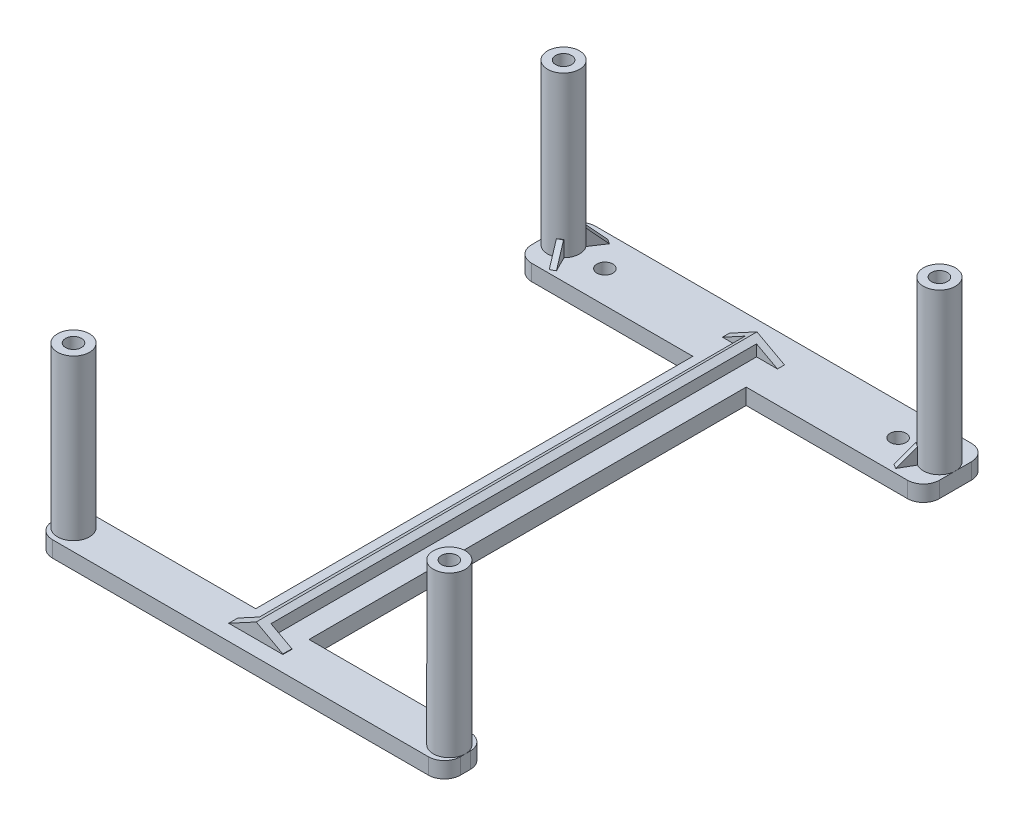
SolidWorks part; units mm, degrees
ref_plane "前视基准面" through (0, 0, 0) normal (0, 0, 1) x (1, 0, 0)
ref_plane "上视基准面" through (0, 0, 0) normal (0, 1, 0) x (1, 0, 0)
ref_plane "右视基准面" through (0, 0, 0) normal (1, 0, 0) x (0, 0, -1)
sketch "草图1" plane through (0, 0, 0) normal (0, 1, 0) x (1, 0, 0)
  line L0 (-39.882, 2.8841) -> (30.618, 2.8841)
  line L1 (-39.882, 2.8841) -> (-39.882, -9.1159)
  line L2 (30.618, 2.8841) -> (30.618, -9.1159)
  line L3 (-39.882, -9.1159) -> (30.618, -9.1159)
  circle A0 centre (-32.132, -3.1159) radius 1.5
  circle A1 centre (22.868, -3.1159) radius 1.5
  dimension "D3" = 3
  dimension "D4" = 6
  dimension "D6" = 3
  dimension "D1" = 12
  dimension "D2" = 70.5
  dimension "D5" = 7.75
  dimension "D7" = 7.75
  dimension "D8" = 6
extrude "凸台-拉伸2" add sketch "草图1" along normal blind 4
sketch "草图3" plane through (0, 0, 0) normal (0, -1, 0) x (1, 0, 0)
  line L2 (-9.632, 91.1159) -> (-9.632, 9.1159)
  line L3 (-9.632, 91.1159) -> (0.368, 91.1159)
  line L4 (-9.632, 9.1159) -> (0.368, 9.1159)
  line L5 (0.368, 91.1159) -> (0.368, 9.1159)
  dimension "D1" = 82
extrude "凸台-拉伸3" add sketch "草图3" against normal blind 3
sketch "草图4" plane through (0, 3, 0) normal (0, 1, 0) x (1, 0, 0)
  line L0 (-4.632, -91.1159) -> (-39.882, -91.1159)
  line L1 (0.368, -91.1159) -> (-9.632, -91.1159) construction
  line L2 (-4.632, -91.1159) -> (30.618, -91.1159)
  line L4 (-39.882, -91.1159) -> (-39.882, -98.9659)
  line L5 (-39.882, -98.9659) -> (30.618, -98.9659)
  line L6 (30.618, -98.9659) -> (30.618, -91.1159)
  dimension "D1" = 35.25
  dimension "D2" = 35.25
  dimension "D3" = 7.85
extrude "凸台-拉伸4" add sketch "草图4" against normal blind 3
sketch "草图5" plane through (0, 4, 0) normal (0, 1, 0) x (1, 0, 0)
  line L0 (-39.882, 2.8841) -> (30.618, 2.8841)
  line L1 (-39.882, 2.8841) -> (-39.882, -9.3325)
  line L2 (30.618, 2.8841) -> (30.618, -9.3325)
  line L3 (-39.882, -9.3325) -> (30.618, -9.3325)
extrude "切除-拉伸1" cut sketch "草图5" against normal blind 1
sketch "草图6" plane through (0, 3, 0) normal (0, 1, 0) x (1, 0, 0)
  line L0 (30.618, -9.1159) -> (30.618, 2.8841) construction
  line L2 (-39.882, 2.8841) -> (-39.882, -9.1159) construction
  line L3 (30.618, -98.9659) -> (30.618, -91.1159) construction
  line L4 (-39.882, -91.1159) -> (-39.882, -98.9659) construction
  circle A0 centre (30.618, -3.1159) radius 3
  circle A1 centre (-39.882, -3.1159) radius 3
  circle A2 centre (30.618, -95.0409) radius 3
  circle A3 centre (-39.882, -95.0409) radius 3
  dimension "D1" = 6
  dimension "D2" = 6
  dimension "D3" = 6
  dimension "D4" = 6
extrude "凸台-拉伸5" add sketch "草图6" along normal blind 30
sketch "草图7" plane through (30.618, 0, 0) normal (1, 0, 0) x (0, 0, -1)
  line L0 (-9.1159, 0) -> (-9.1159, 3)
  line L1 (-9.1159, 0) -> (2.8841, 0)
  line L2 (-9.1159, 3) -> (2.8841, 3)
  line L3 (2.8841, 0) -> (2.8841, 3)
  dimension "D1" = 12
extrude "凸台-拉伸6" add sketch "草图7" along normal blind 3
sketch "草图8" plane through (-39.882, 0, 0) normal (-1, 0, 0) x (0, 0, 1)
  line L0 (-2.8841, 0) -> (-2.8841, 3)
  line L1 (-2.8841, 0) -> (9.1159, 0)
  line L2 (-2.8841, 3) -> (9.1159, 3)
  line L3 (9.1159, 0) -> (9.1159, 3)
  dimension "D1" = 12
extrude "凸台-拉伸7" add sketch "草图8" along normal blind 3
sketch "草图10" plane through (30.618, 0, 0) normal (1, 0, 0) x (0, 0, -1)
  line L0 (-98.9659, 0) -> (-98.9659, 3)
  line L1 (-98.9659, 0) -> (-91.1159, 0)
  line L2 (-98.9659, 3) -> (-91.1159, 3)
  line L3 (-91.1159, 0) -> (-91.1159, 3)
  dimension "D1" = 7.85
extrude "凸台-拉伸8" add sketch "草图10" along normal blind 3
sketch "草图11" plane through (-39.882, 0, 0) normal (-1, 0, 0) x (0, 0, 1)
  line L0 (91.1159, 0) -> (91.1159, 3)
  line L1 (91.1159, 0) -> (98.9659, 0)
  line L2 (91.1159, 3) -> (98.9659, 3)
  line L3 (98.9659, 0) -> (98.9659, 3)
  dimension "D1" = 7.85
extrude "凸台-拉伸9" add sketch "草图11" along normal blind 3
fillet "圆角1" radius 3 8 edges at (-42.882, 1.5, 9.1159) (-42.882, 1.5, -2.8841) (33.618, 1.5, -2.8841) (33.618, 1.5, 9.1159) (33.618, 1.5, 91.1159) (33.618, 1.5, 98.9659) (-42.882, 1.5, 91.1159) (-42.882, 1.5, 98.9659)
sketch "草图12" plane through (0, 3, 0) normal (0, 1, 0) x (1, 0, 0)
  line L0 (-39.882, -3.1159) -> (-36.5744, 1.8901)
  line L1 (-39.882, -3.1159) -> (-37.2005, -8.4833)
  line L2 (-36.5744, 1.8901) -> (-35.7401, 1.3389)
  line L3 (-35.7401, 1.3389) -> (-38.7294, -3.1854)
  line L4 (-38.7294, -3.1854) -> (-36.3059, -8.0364)
  line L5 (-36.3059, -8.0364) -> (-37.2005, -8.4833)
  line L6 (30.618, -3.1159) -> (27.618, 2.0803)
  line L7 (30.618, -3.1159) -> (27.618, -8.312)
  line L9 (27.618, 2.0803) -> (26.8002, 1.5047)
  line L10 (26.8002, 1.5047) -> (29.4872, -3.1159)
  line L11 (27.618, -8.312) -> (26.7656, -7.7892)
  line L12 (26.7656, -7.7892) -> (29.4872, -3.1159)
  line L13 (-9.9605, -3.2364) -> (-5.7145, -3.2364)
  line L16 (-9.9605, -1.9208) -> (0, -1.9208)
  line L17 (-9.9605, -1.9208) -> (-9.9605, -3.2364)
  line L18 (0, -1.9208) -> (0.359, -1.9208)
  line L19 (0.359, -1.9208) -> (0.359, -3.2364)
  line L20 (0.359, -3.2364) -> (-3.5616, -3.2364)
  line L21 (-5.7145, -3.2364) -> (-5.7145, -94.3184)
  line L22 (-3.5616, -3.2364) -> (-3.5616, -94.3184)
  line L23 (-9.9605, -94.3184) -> (-5.7145, -94.3184)
  line L24 (-3.5616, -94.3184) -> (0.359, -94.3184)
  line L25 (-9.9605, -94.3184) -> (-9.9605, -96.0146)
  line L26 (0.359, -94.3184) -> (0.359, -96.0146)
  line L27 (-9.9605, -96.0146) -> (0.359, -96.0146)
  dimension "D1" = 120
  dimension "D2" = 6
  dimension "D3" = 6
  dimension "D4" = 1
  dimension "D5" = 1
  dimension "D8" = 1
  dimension "D9" = 6
  dimension "D10" = 6
  dimension "D11" = 1
extrude "凸台-拉伸10" add sketch "草图12" along normal blind 3
sketch "草图13" plane through (-25.495, 0, -16.845) normal (0.8343, 0, 0.5513) x (0.5513, 0, -0.8343)
  line L0 (-21.7566, 6) -> (-18.585, 3)
  line L1 (-18.585, 3) -> (-18.585, 6)
  line L2 (-18.585, 6) -> (-21.7566, 6)
sketch "草图14" plane through (-10.2451, 0, 15.5061) normal (0.5513, 0, -0.8343) x (-0.8343, 0, -0.5513)
  line L0 (30.5573, 3) -> (31.5573, 3)
sweep "切除-扫描1" cut profiles "草图13" path "草图14"
sketch "草图15" plane through (-33.1616, 0, 16.5675) normal (-0.8946, 0, 0.4469) x (0.4469, 0, 0.8946)
  line L0 (-12.0369, 6) -> (-9.0369, 3)
  line L1 (-9.0369, 6) -> (-9.0369, 3) construction
  line L2 (-12.0369, 3) -> (-9.0369, 3) construction
  line L3 (-9.0369, 3) -> (-9.0369, 6)
  line L4 (-9.0369, 6) -> (-12.0369, 6)
sketch "草图16" plane through (-4.0388, 0, -8.0841) normal (0.4469, 0, 0.8946) x (0.8946, 0, -0.4469)
  line L0 (-37.0699, 3) -> (-36.0699, 3)
sweep "切除-扫描2" cut profiles "草图15" path "草图16"
sketch "草图17" plane through (21.6143, 0, -12.479) normal (0.866, 0, -0.5) x (-0.5, 0, -0.866)
  line L0 (-15.0074, 6) -> (-12.0074, 3)
  line L1 (-12.0074, 3) -> (-12.0074, 6)
  line L2 (-12.0074, 6) -> (-15.0074, 6)
sketch "草图18" plane through (8.1696, 0, 11.6077) normal (-0.5755, 0, -0.8178) x (-0.8178, 0, 0.5755)
  line L0 (-23.7824, 3) -> (-22.7824, 3)
sweep "切除-扫描3" cut profiles "草图17" path "草图18"
sketch "草图19" plane through (24.3127, 0, 14.037) normal (0.866, 0, 0.5) x (0.5, 0, -0.866)
  line L0 (9.6106, 6) -> (6.6106, 3)
  line L1 (6.6106, 6) -> (9.6106, 6) construction
  line L2 (9.6106, 3) -> (9.6106, 6) construction
  line L3 (6.6106, 3) -> (6.6106, 6)
  line L4 (6.6106, 6) -> (9.6106, 6)
sketch "草图20" plane through (3.8462, 0, -6.2701) normal (-0.5229, 0, 0.8524) x (0.8524, 0, 0.5229)
  line L0 (27.8879, 3) -> (26.8879, 3)
sweep "切除-扫描4" cut profiles "草图19" path "草图20"
sketch "草图24" plane through (0, 0, 1.9208) normal (0, 0, -1) x (-1, 0, 0)
  line L0 (-0.359, 3) -> (4.8008, 5.7899)
  line L1 (4.8008, 5.7899) -> (9.9605, 3)
  line L2 (-0.359, 3) -> (-0.359, 6)
  line L3 (-0.359, 6) -> (10.1096, 6)
  line L4 (10.1096, 6) -> (10.6819, 6)
  line L5 (-30.618, 3) -> (39.882, 3) construction
  line L6 (10.1096, 3) -> (9.9605, 3)
  line L7 (10.6819, 6) -> (10.6819, 3)
  line L8 (10.6819, 3) -> (10.1096, 3)
sketch "草图25" plane through (0, 3, 0) normal (0, 1, 0) x (1, 0, 0)
  line L0 (-4.8008, -1.9208) -> (-4.632, -98.9659)
  line L1 (-4.8008, -1.9208) -> (-9.9605, -1.9208) construction
  line L2 (0.359, -1.9208) -> (-4.8008, -1.9208) construction
  line L3 (-39.882, -98.9659) -> (30.618, -98.9659) construction
sweep "切除-扫描8" cut profiles "草图24" path "草图25"
sketch "草图26" plane through (0, 33, 0) normal (0, 1, 0) x (1, 0, 0)
  circle A0 centre (-39.882, -95.0409) radius 1.5
  dimension "D1" = 3
extrude "切除-拉伸2" cut sketch "草图26" against normal blind 30
sketch "草图28" plane through (0, 33, 0) normal (0, 1, 0) x (1, 0, 0)
  circle A0 centre (30.618, -95.0409) radius 1.5
  dimension "D1" = 3
extrude "切除-拉伸3" cut sketch "草图28" against normal blind 30
sketch "草图29" plane through (0, 33, 0) normal (0, 1, 0) x (1, 0, 0)
  circle A0 centre (-39.882, -3.1159) radius 1.5
  dimension "D1" = 3
sketch "草图30" plane through (0, 33, 0) normal (0, 1, 0) x (1, 0, 0)
  circle A0 centre (30.618, -3.1159) radius 1.5
  dimension "D1" = 3
extrude "切除-拉伸4" cut sketch "草图30" against normal blind 30
extrude "切除-拉伸5" cut sketch "草图29" against normal blind 30 contours A0
